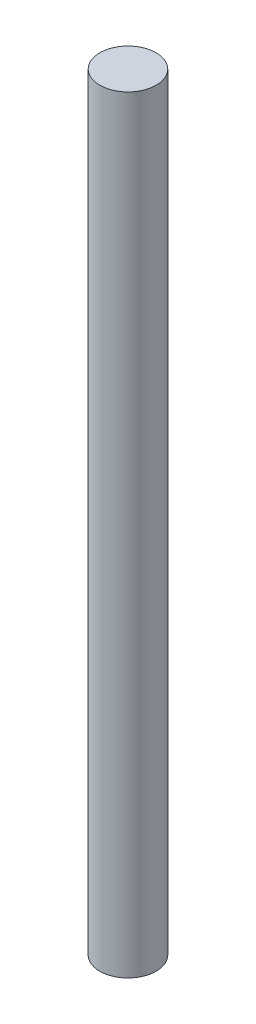
SolidWorks part; units mm, degrees
ref_plane "Alzado" through (0, 0, 0) normal (0, 0, 1) x (1, 0, 0)
ref_plane "Planta" through (0, 0, 0) normal (0, 1, 0) x (1, 0, 0)
ref_plane "Vista lateral" through (0, 0, 0) normal (1, 0, 0) x (0, 0, -1)
sketch "Croquis1" plane through (0, 0, 0) normal (0, 1, 0) x (1, 0, 0)
  circle A0 centre (0, 0) radius 3.165
  dimension "D1" = 6.33
extrude "Saliente-Extruir1" add sketch "Croquis1" along normal blind 86.28
